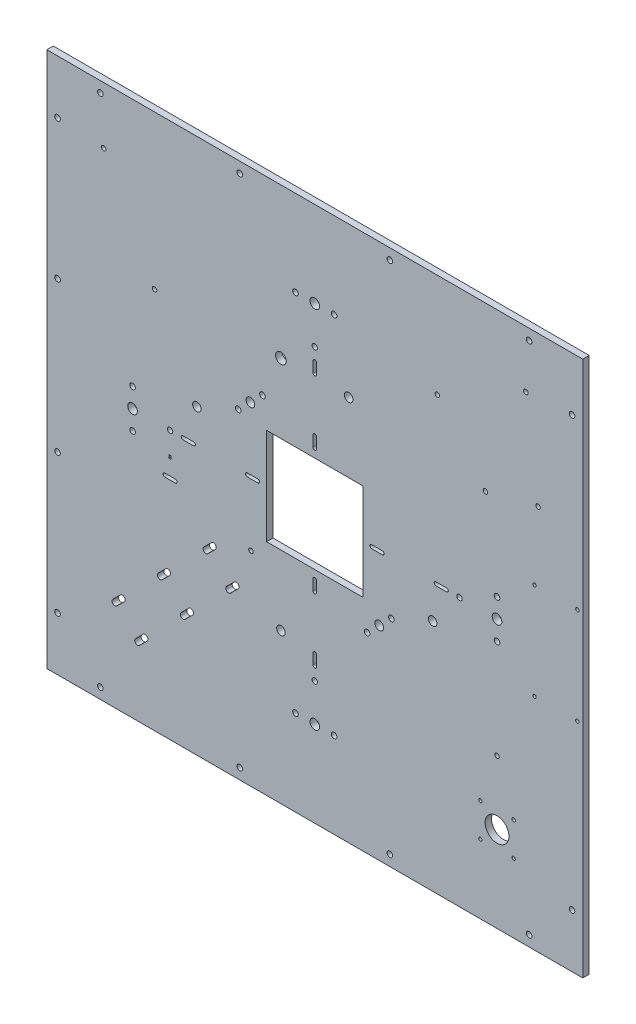
SolidWorks part; units mm, degrees
ref_plane "前视基准面" through (0, 0, 0) normal (0, 0, 1) x (1, 0, 0)
ref_plane "上视基准面" through (0, 0, 0) normal (0, 1, 0) x (1, 0, 0)
ref_plane "右视基准面" through (0, 0, 0) normal (1, 0, 0) x (0, 0, -1)
sketch "草图1" plane through (0, 0, 0) normal (0, 0, 1) x (1, 0, 0)
  line L0 (0, 0) -> (500, -500) construction
  line L1 (0, 0) -> (500, 0)
  line L2 (0, 0) -> (0, -500)
  line L3 (0, -500) -> (500, -500)
  line L4 (500, 0) -> (500, -500)
  line L5 (0, -500) -> (500, 0) construction
  dimension "D1" = 500
  dimension "D2" = 500
extrude "凸台-拉伸1" add sketch "草图1" along normal blind 6
sketch "草图2" plane through (0, 0, 6) normal (0, 0, 1) x (1, 0, 0)
  line L0 (0, 0) -> (500, -500) construction
  line L1 (500, 0) -> (0, -500) construction
  line L3 (205, -205) -> (295, -205)
  line L4 (205, -205) -> (205, -295)
  line L5 (205, -295) -> (295, -295)
  line L6 (295, -205) -> (295, -295)
  line L7 (205, -205) -> (295, -295) construction
  line L8 (205, -295) -> (295, -205) construction
  point P8 (250, -250)
  dimension "D1" = 90
extrude "切除-中心方孔" cut sketch "草图2" against normal through all
sketch "草图3" plane through (0, 0, 6) normal (0, 0, 1) x (1, 0, 0)
  line L0 (0, 0) -> (500, -500) construction
  line L1 (500, 0) -> (0, -500) construction
  line L2 (250, -250) -> (-100.3475, -250) construction
  line L3 (250, -250) -> (250, 21.0632) construction
  line L4 (250, -137) -> (250, -127) construction
  line L5 (248.4, -137) -> (248.4, -127)
  line L6 (250, -197) -> (250, -187) construction
  line L7 (248.4, -197) -> (248.4, -187)
  line L8 (251.6, -197) -> (251.6, -187)
  line L9 (295, -205) -> (205, -205) construction
  line L10 (251.6, -137) -> (251.6, -127)
  line L11 (250, -303) -> (250, -313) construction
  line L12 (248.4, -303) -> (248.4, -313)
  line L13 (251.6, -303) -> (251.6, -313)
  line L14 (250, -363) -> (250, -373) construction
  line L15 (248.4, -363) -> (248.4, -373)
  line L16 (251.6, -363) -> (251.6, -373)
  line L17 (187, -250) -> (197, -250) construction
  line L18 (187, -248.4) -> (197, -248.4)
  line L19 (187, -251.6) -> (197, -251.6)
  line L20 (137, -250) -> (127, -250) construction
  line L21 (137, -251.6) -> (127, -251.6)
  line L22 (137, -248.4) -> (127, -248.4)
  line L23 (205, -205) -> (205, -295) construction
  line L24 (313, -250) -> (303, -250) construction
  line L25 (313, -248.4) -> (303, -248.4)
  line L26 (313, -251.6) -> (303, -251.6)
  line L27 (363, -250) -> (373, -250) construction
  line L28 (363, -251.6) -> (373, -251.6)
  line L29 (363, -248.4) -> (373, -248.4)
  arc A8 (248.4, -197) -> (251.6, -197) centre (250, -197) ccw
  arc A9 (251.6, -187) -> (248.4, -187) centre (250, -187) ccw
  arc A10 (248.4, -137) -> (251.6, -137) centre (250, -137) ccw
  arc A11 (251.6, -127) -> (248.4, -127) centre (250, -127) ccw
  arc A12 (248.4, -303) -> (251.6, -303) centre (250, -303) cw
  arc A13 (251.6, -313) -> (248.4, -313) centre (250, -313) cw
  arc A14 (248.4, -363) -> (251.6, -363) centre (250, -363) cw
  arc A15 (251.6, -373) -> (248.4, -373) centre (250, -373) cw
  arc A16 (187, -248.4) -> (187, -251.6) centre (187, -250) ccw
  arc A17 (197, -251.6) -> (197, -248.4) centre (197, -250) ccw
  arc A18 (137, -251.6) -> (137, -248.4) centre (137, -250) ccw
  arc A19 (127, -248.4) -> (127, -251.6) centre (127, -250) ccw
  arc A20 (313, -248.4) -> (313, -251.6) centre (313, -250) cw
  arc A21 (303, -251.6) -> (303, -248.4) centre (303, -250) cw
  arc A22 (363, -251.6) -> (363, -248.4) centre (363, -250) cw
  arc A23 (373, -248.4) -> (373, -251.6) centre (373, -250) cw
  point P13 (250, -192)
  point P22 (250, -132)
  point P29 (250, -308)
  point P36 (250, -368)
  point P43 (192, -250)
  point P48 (132, -250)
  point P59 (308, -250)
  point P66 (368, -250)
  dimension "D1" = 1.6
  dimension "D2" = 10
  dimension "D5" = 10
  dimension "D6" = 60
  dimension "D4" = 1.6
  dimension "D7" = 1.6
  dimension "D8" = 1.6
  dimension "D3" = 8
  dimension "D9" = 10
  dimension "D10" = 10
  dimension "D11" = 8
  dimension "D12" = 60
extrude "切除-滑轨安装孔" cut sketch "草图3" against normal through all
sketch "草图4" plane through (0, 0, 6) normal (0, 0, 1) x (1, 0, 0)
  line L0 (205, -205) -> (295, -295) construction
  line L1 (295, -205) -> (205, -295) construction
  line L2 (250, -250) -> (552.3477, -250) construction
  line L3 (250, -250) -> (250, -26.8713) construction
  circle A0 centre (420, -250) radius 4.5
  circle A1 centre (420, -268) radius 2.6
  circle A2 centre (420, -232) radius 2.6
  circle A4 centre (250, -420) radius 4.5
  circle A5 centre (232, -420) radius 2.6
  circle A6 centre (268, -420) radius 2.6
  circle A7 centre (80, -250) radius 4.5
  circle A8 centre (80, -232) radius 2.6
  circle A9 centre (80, -268) radius 2.6
  circle A10 centre (250, -80) radius 4.5
  circle A11 centre (268, -80) radius 2.6
  circle A12 centre (232, -80) radius 2.6
  point P38 (250, -250)
  dimension "D1" = 9
  dimension "D2" = 5.2
  dimension "D3" = 18
  dimension "D4" = 170
  dimension "D5" = 4
extrude "切除-轴承座安装孔" cut sketch "草图4" against normal through all
sketch "草图5" plane through (0, 0, 0) normal (0, 0, -1) x (-1, 0, 0)
  line L0 (-250, -420) -> (-666.0384, -420) construction
  line L1 (-420, -250) -> (-420, -420) construction
  line L2 (-435.5, -404.5) -> (-404.5, -404.5) construction
  line L3 (-250, -420) -> (-250, 31.5665) construction
  line L4 (0, 0) -> (0, -500) construction
  line L5 (-404.5, -404.5) -> (-404.5, -435.5) construction
  circle A0 centre (-420, -420) radius 11.1
  circle A12 centre (-435.5, -404.5) radius 1.6
  circle A13 centre (-435.5, -435.5) radius 1.55
  circle A14 centre (-404.5, -435.5) radius 1.55
  circle A15 centre (-404.5, -404.5) radius 1.55
  dimension "D1" = 250
  dimension "D2" = 15.5
  dimension "D7" = 15.5
  dimension "D3" = 15.5
  dimension "D4" = 31
  dimension "D5" = 31
  dimension "D6" = 31
sketch "草图6" plane through (0, 0, 0) normal (0, 0, -1) x (-1, 0, 0)
  line L0 (-205, -205) -> (-205, -295) construction
  line L1 (-205, -205) -> (-205, -295) construction
  line L2 (-205, -295) -> (-295, -295) construction
  line L3 (-205, -295) -> (-295, -295) construction
  line L12 (-205, -295) -> (-259.3282, -240.805) construction
  line L13 (-176.655, -344.4627) -> (-169.5753, -351.5251) construction
  line L14 (-174.8188, -342.622) -> (-167.739, -349.6844)
  line L15 (-178.4912, -346.3035) -> (-171.4115, -353.3658)
  line L16 (-91.6981, -429.2113) -> (-84.6183, -436.2737) construction
  line L17 (-89.8619, -427.3706) -> (-82.7821, -434.433)
  line L18 (-93.5343, -431.052) -> (-86.4546, -438.1144)
  line L19 (-176.655, -344.4627) -> (-169.5753, -351.5251) construction
  line L20 (-70.5109, -407.9721) -> (-63.4312, -415.0345) construction
  line L21 (-72.3472, -409.8128) -> (-65.2674, -416.8752)
  line L22 (-68.6747, -406.1314) -> (-61.595, -413.1937)
  line L23 (-155.4678, -323.2235) -> (-148.3881, -330.2859) construction
  line L24 (-157.3041, -325.0642) -> (-150.2243, -332.1266)
  line L25 (-153.6316, -321.3828) -> (-146.5519, -328.4451)
  line L26 (-151.928, -326.7547) -> (-173.1151, -347.9939) construction
  line L27 (-134.2242, -386.8848) -> (-127.1532, -393.9559) construction
  line L28 (-132.3858, -385.0463) -> (-125.3147, -392.1174)
  line L29 (-136.0627, -388.7233) -> (-128.9917, -395.7943)
  line L30 (-173.1151, -347.9939) -> (-130.6887, -390.4203) construction
  line L31 (-500, 0) -> (0, -500) construction
  line L32 (-112.9417, -365.55) -> (-105.8533, -372.6037) construction
  line L33 (-114.7757, -367.3929) -> (-107.6873, -374.4466)
  line L34 (-111.1078, -363.707) -> (-104.0194, -370.7607)
  arc A0 (-174.8188, -342.622) -> (-178.4912, -346.3035) centre (-176.655, -344.4627) ccw
  arc A1 (-171.4115, -353.3658) -> (-167.739, -349.6844) centre (-169.5753, -351.5251) ccw
  arc A2 (-89.8619, -427.3706) -> (-93.5343, -431.052) centre (-91.6981, -429.2113) ccw
  arc A3 (-86.4546, -438.1144) -> (-82.7821, -434.433) centre (-84.6183, -436.2737) ccw
  arc A4 (-72.3472, -409.8128) -> (-68.6747, -406.1314) centre (-70.5109, -407.9721) cw
  arc A5 (-61.595, -413.1937) -> (-65.2674, -416.8752) centre (-63.4312, -415.0345) cw
  arc A6 (-157.3041, -325.0642) -> (-153.6316, -321.3828) centre (-155.4678, -323.2235) cw
  arc A7 (-146.5519, -328.4451) -> (-150.2243, -332.1266) centre (-148.3881, -330.2859) cw
  arc A8 (-132.3858, -385.0463) -> (-136.0627, -388.7233) centre (-134.2242, -386.8848) ccw
  arc A9 (-128.9917, -395.7943) -> (-125.3147, -392.1174) centre (-127.1532, -393.9559) ccw
  arc A10 (-114.7757, -367.3929) -> (-111.1078, -363.707) centre (-112.9417, -365.55) cw
  arc A11 (-104.0194, -370.7607) -> (-107.6873, -374.4466) centre (-105.8533, -372.6037) cw
  point P10 (-173.1151, -347.9939)
  point P16 (-88.1582, -432.7425)
  point P26 (-66.9711, -411.5033)
  point P33 (-151.928, -326.7547)
  point P38 (-130.6887, -390.4203)
  point P48 (-109.3975, -369.0768)
  dimension "D2" = 2.6
  dimension "D3" = 2.6
  dimension "D8" = 10
  dimension "D9" = 2.6
  dimension "D4" = 10
  dimension "D5" = 10
  dimension "D6" = 120
  dimension "D1" = 30
  dimension "D7" = 60
  dimension "D10" = 60
extrude "切除-现有滑轨固定座安装孔" cut sketch "草图6" against normal through all
sketch "草图7" plane through (0, 0, 0) normal (0, 0, -1) x (-1, 0, 0)
  line L0 (0, 0) -> (-500, -500) construction
  line L1 (-500, 0) -> (0, -500) construction
  line L2 (-310.1041, -310.1041) -> (-298.7904, -321.4178) construction
  circle A0 centre (-310.1041, -310.1041) radius 4.05
  circle A1 centre (-298.7904, -321.4178) radius 2.6
  circle A2 centre (-178.5822, -201.2096) radius 2.6
  circle A3 centre (-189.8959, -189.8959) radius 4.05
  circle A4 centre (-201.2096, -178.5822) radius 2.6
  circle A5 centre (-321.4178, -298.7904) radius 2.6
  dimension "D1" = 8.1
  dimension "D2" = 5.2
  dimension "D3" = 32
  dimension "D4" = 170
extrude "切除-光轴固定座安装孔" cut sketch "草图7" against normal through all
sketch "草图8" plane through (0, 0, 0) normal (0, 0, -1) x (-1, 0, 0)
  line L0 (-500, 0) -> (0, -500) construction
  line L1 (0, 0) -> (-500, -500) construction
  line L2 (-250, -250) -> (-250, 13.5792) construction
  line L3 (-250, -250) -> (-619.5254, -250) construction
  line L4 (-500, -500) -> (-500, 0) construction
  line L5 (-500, 0) -> (0, 0) construction
  line L6 (-10, -50) -> (-10, -180) construction
  line L7 (-10, -320) -> (-10, -450) construction
  circle A0 centre (-450, -10) radius 2.6
  circle A1 centre (-320, -10) radius 2.6
  circle A2 centre (-490, -50) radius 2.6
  circle A4 centre (-180, -10) radius 2.6
  circle A5 centre (-50, -10) radius 2.6
  circle A6 centre (-10, -180) radius 2.6
  circle A7 centre (-10, -50) radius 2.6
  circle A9 centre (-490, -450) radius 2.6
  circle A10 centre (-10, -320) radius 2.6
  circle A11 centre (-10, -450) radius 2.6
  circle A12 centre (-50, -490) radius 2.6
  circle A13 centre (-180, -490) radius 2.6
  circle A14 centre (-320, -490) radius 2.6
  circle A15 centre (-450, -490) radius 2.6
  dimension "D1" = 5.2
  dimension "D2" = 5.2
  dimension "D3" = 5.2
  dimension "D4" = 130
  dimension "D5" = 130
  dimension "D6" = 50
  dimension "D7" = 10
  dimension "D8" = 50
  dimension "D9" = 10
  dimension "D12" = 10
extrude "切除-铝型材固定孔" cut sketch "草图8" against normal through all
extrude "切除-步进电机安装孔" cut sketch "草图5" against normal through all
sketch "草图9" plane through (0, 0, 0) normal (0, 0, -1) x (-1, 0, 0)
  line L0 (-205, -205) -> (-295, -205) construction
  line L1 (-250, -250) -> (-250, 47.4716) construction
  line L2 (0, 0) -> (-500, -500) construction
  line L3 (-250, -250) -> (65.3261, -250) construction
  circle A0 centre (-250, -115) radius 2.5
  circle A2 centre (-115, -250) radius 2.5
  circle A3 centre (-250, -385) radius 2.5
  circle A4 centre (-385, -250) radius 2.5
  point P18 (-250, -250)
  dimension "D1" = 5
  dimension "D2" = 90
  dimension "D3" = 4
extrude "切除-便于安装步进电机支架的孔" cut sketch "草图9" against normal through all
sketch "草图10" plane through (0, 0, 0) normal (0, 0, -1) x (-1, 0, 0)
  line L0 (-250, -250) -> (-250, 22.025) construction
  line L1 (-295, -5) -> (-295, -45) construction
  line L2 (-500, 0) -> (0, 0) construction
  line L3 (-500, 0) -> (-250, -250) construction
  circle A4 centre (-495, -295) radius 1.6
  circle A5 centre (-455, -295) radius 1.6
  circle A6 centre (-455, -205) radius 1.6
  circle A7 centre (-495, -205) radius 1.6
  dimension "D3" = 40
  dimension "D5" = 5
extrude "切除-mark安装孔" cut sketch "草图10" against normal through all
sketch "草图11" plane through (0, 0, 0) normal (0, 0, -1) x (-1, 0, 0)
  line L0 (-120, -288.6) -> (-110, -288.6) construction
  line L1 (-120, -287) -> (-110, -287)
  line L2 (-120, -290.2) -> (-110, -290.2)
  line L3 (-127, -251.6) -> (-137, -251.6) construction
  line L4 (0, 0) -> (0, -500) construction
  line L5 (-115, -271.6) -> (-115, -288.6) construction
  line L6 (-116, -270.1) -> (-114, -270.1)
  line L7 (-116, -270.1) -> (-116, -273.1)
  line L8 (-116, -273.1) -> (-114, -273.1)
  line L9 (-114, -270.1) -> (-114, -273.1)
  line L10 (-116, -270.1) -> (-114, -273.1) construction
  line L11 (-116, -273.1) -> (-114, -270.1) construction
  arc A0 (-120, -287) -> (-120, -290.2) centre (-120, -288.6) ccw
  arc A1 (-110, -290.2) -> (-110, -287) centre (-110, -288.6) ccw
  point P2 (-115, -288.6)
  point P11 (-115, -271.6)
  dimension "D1" = 1.6
  dimension "D2" = 10
  dimension "D3" = 37
  dimension "D4" = 115
  dimension "D5" = 3
  dimension "D6" = 2
  dimension "D7" = 17
extrude "切除-水平导轨限位开关支架安装孔" cut sketch "草图11" against normal through all
sketch "草图12" plane through (0, 0, 0) normal (0, 0, -1) x (-1, 0, 0)
  line L0 (-500, 0) -> (0, 0) construction
  line L1 (-251.6, -137) -> (-251.6, -127) construction
  circle A0 centre (-281.6, -140) radius 4
  circle A1 centre (-360, -281.6) radius 4
  circle A2 centre (-218.4, -360) radius 4
  circle A3 centre (-140, -218.4) radius 4
  point P15 (-250, -250)
  dimension "D1" = 8
  dimension "D2" = 140
  dimension "D3" = 30
  dimension "D4" = 4
extrude "切除-步进电机走线孔" cut sketch "草图12" against normal through all
sketch "草图13" plane through (0, 0, 0) normal (0, 0, -1) x (-1, 0, 0)
  line L0 (-500, 0) -> (0, -500) construction
  line L1 (0, 0) -> (-500, -500) construction
  line L2 (-140, -218.4) -> (-53.033, -53.033) construction
  line L3 (-218.4, -360) -> (-140, -218.4) construction
  line L4 (-281.6, -140) -> (-446.967, -53.033) construction
  line L5 (-360, -281.6) -> (-446.967, -53.033) construction
  line L6 (-420, -360.4854) -> (-458.2485, -140) construction
  circle A0 centre (-420, -360.4854) radius 2.1
  circle A1 centre (-446.967, -53.033) radius 2.1
  circle A2 centre (-53.033, -53.033) radius 2.1
  circle A3 centre (-190.4611, -309.5389) radius 2.1
  circle A4 centre (-100.5137, -143.3171) radius 2.1
  circle A5 centre (-458.2485, -140) radius 2.1
  circle A6 centre (-364.2835, -96.5165) radius 2.1
  circle A7 centre (-409.2154, -152.2518) radius 2.1
  dimension "D1" = 4.2
  dimension "D4" = 4.2
  dimension "D5" = 4.2
  dimension "D6" = 4.2
  dimension "D7" = 4.2
  dimension "D8" = 4.2
  dimension "D9" = 4.2
  dimension "D10" = 4.2
  dimension "D2" = 75
  dimension "D3" = 75
extrude "切除-拉伸3" cut sketch "草图13" against normal through all
sketch "草图14" plane through (0, 0, 0) normal (0, 0, -1) x (-1, 0, 0)
  line L0 (-281.6, -140) -> (-218.4, -140) construction
  line L1 (-250, -137) -> (-250, -140) construction
  circle A0 centre (-218.4, -140) radius 5
  dimension "D1" = 10
extrude "切除-拉伸4" cut sketch "草图14" against normal through all
